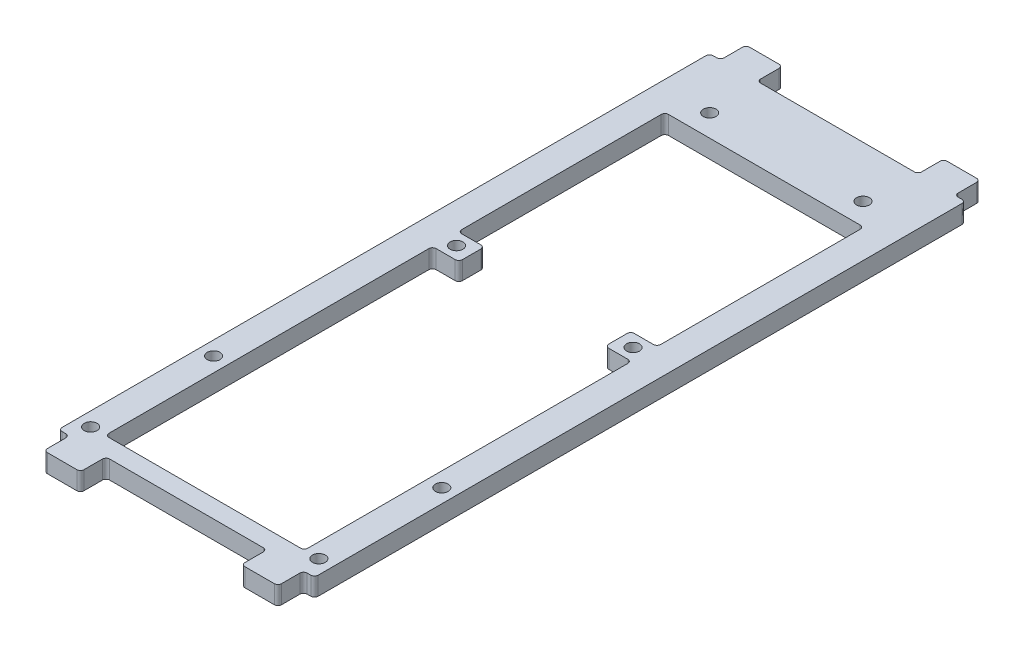
SolidWorks part; units mm, degrees
material "Acrylic (Medium-high impact)"
ref_plane "Front Plane" through (0, 0, 0) normal (0, 0, 1) x (1, 0, 0)
ref_plane "Top Plane" through (0, 0, 0) normal (0, 1, 0) x (1, 0, 0)
ref_plane "Right Plane" through (0, 0, 0) normal (1, 0, 0) x (0, 0, -1)
sketch "Sketch1" plane through (0, 0, 0) normal (0, 1, 0) x (1, 0, 0)
  line L0 (0, 0) -> (0, 34.093) construction
  line L5 (34, -89) -> (33, -89)
  line L6 (35, -88) -> (35, 88)
  line L27 (34, 89) -> (33, 89)
  line L28 (-35, -88) -> (-35, 88)
  line L29 (35, -89) -> (-35, 89) construction
  line L30 (35, 89) -> (-35, -89) construction
  line L32 (-32, 90) -> (-32, 95)
  line L33 (-31, 96) -> (-23, 96)
  line L34 (-22, 90) -> (-22, 95)
  line L35 (0, 0) -> (-23.5471, 0) construction
  line L36 (31, 96) -> (23, 96)
  line L37 (22, 90) -> (22, 95)
  line L38 (32, 90) -> (32, 95)
  line L39 (21, 89) -> (-21, 89)
  line L40 (-33, 89) -> (-34, 89)
  line L41 (32, -90) -> (32, -95)
  line L42 (31, -96) -> (23, -96)
  line L43 (22, -90) -> (22, -95)
  line L44 (-22, -90) -> (-22, -95)
  line L45 (-31, -96) -> (-23, -96)
  line L46 (-32, -90) -> (-32, -95)
  line L47 (-33, -89) -> (-34, -89)
  line L48 (21, -89) -> (-21, -89)
  arc A0 (22, -90) -> (21, -89) centre (21, -90) ccw
  arc A1 (23, -96) -> (22, -95) centre (23, -95) cw
  arc A2 (32, -95) -> (31, -96) centre (31, -95) cw
  arc A3 (32, -90) -> (33, -89) centre (33, -90) cw
  arc A4 (34, -89) -> (35, -88) centre (34, -88) ccw
  arc A5 (35, 88) -> (34, 89) centre (34, 88) ccw
  arc A6 (32, 90) -> (33, 89) centre (33, 90) ccw
  arc A7 (31, 96) -> (32, 95) centre (31, 95) cw
  arc A8 (23, 96) -> (22, 95) centre (23, 95) ccw
  arc A9 (22, 90) -> (21, 89) centre (21, 90) cw
  arc A10 (-21, 89) -> (-22, 90) centre (-21, 90) cw
  arc A11 (-23, 96) -> (-22, 95) centre (-23, 95) cw
  arc A12 (-32, 95) -> (-31, 96) centre (-31, 95) cw
  arc A13 (-33, 89) -> (-32, 90) centre (-33, 90) ccw
  arc A14 (-34, 89) -> (-35, 88) centre (-34, 88) ccw
  arc A15 (-34, -89) -> (-35, -88) centre (-34, -88) cw
  arc A16 (-32, -90) -> (-33, -89) centre (-33, -90) ccw
  arc A17 (-22, -90) -> (-21, -89) centre (-21, -90) cw
  arc A18 (-22, -95) -> (-23, -96) centre (-23, -95) cw
  arc A19 (-31, -96) -> (-32, -95) centre (-31, -95) cw
  point P0 (0, 0)
  point P27 (22, -89)
  point P30 (22, -96)
  point P33 (32, -96)
  point P36 (32, -89)
  point P45 (32, 89)
  point P48 (32, 96)
  point P51 (22, 96)
  point P54 (22, 89)
  point P57 (-22, 89)
  point P60 (-22, 96)
  point P63 (-32, 96)
  point P66 (-32, 89)
  point P75 (-32, -89)
  point P78 (-22, -89)
  point P81 (-22, -96)
  point P84 (-32, -96)
  dimension "D6" = 1
  dimension "D1" = 70
  dimension "D2" = 178
  dimension "D3" = 7
  dimension "D4" = 10
  dimension "D5" = 3
extrude "Boss-Extrude1" add sketch "Sketch1" along normal blind 5
sketch "Sketch2" plane through (0, 5, 0) normal (0, 1, 0) x (1, 0, 0)
  line L0 (0, 0) -> (0, -23.9489) construction
  circle A0 centre (-20.955, 75) radius 1.75
  circle A1 centre (-24.13, 8.96) radius 1.75
  circle A2 centre (20.955, 75) radius 1.75
  circle A3 centre (24.13, 8.96) radius 1.75
  dimension "D1" = 3.5
  dimension "D2" = 20.955
  dimension "D4" = 3.5
  dimension "D3" = 75
  dimension "D5" = 3.175
  dimension "D6" = 66.04
extrude "Cut-Extrude1" cut sketch "Sketch2" against normal blind 10
sketch "Sketch3" plane through (0, 5, 0) normal (0, 1, 0) x (1, 0, 0)
  line L0 (-21, -89) -> (21, -89) construction
  line L1 (-35, 88) -> (-35, -88) construction
  circle A0 centre (-31.2, -84) radius 1.75
  circle A1 centre (31.2, -84) radius 1.75
  circle A2 centre (31.2, -50.4) radius 1.75
  circle A3 centre (-31.2, -50.4) radius 1.75
  dimension "D1" = 3.5
  dimension "D2" = 5
  dimension "D3" = 3.8
  dimension "D4" = 2
  dimension "D5" = 2
extrude "Cut-Extrude2" cut sketch "Sketch3" against normal blind 10
sketch "Sketch4" plane through (0, 5, 0) normal (0, 1, 0) x (1, 0, 0)
  line L1 (-31.2, -84) -> (31.2, -84) construction
  line L2 (-31.2, -84) -> (-31.2, -50.4) construction
  line L3 (-31.2, -50.4) -> (31.2, -50.4) construction
  line L4 (31.2, -84) -> (31.2, -50.4) construction
  line L5 (-26.2, -84) -> (26.2, -84)
  line L6 (-27.2, -83) -> (-27.2, -72.4)
  line L7 (-27.2, -50.4) -> (27.2, -50.4)
  line L16 (-27.2, -50.4) -> (-27.2, -72.4)
  line L17 (27.2, -50.4) -> (27.2, -83)
  arc A0 (26.2, -84) -> (27.2, -83) centre (26.2, -83) ccw
  arc A1 (-26.2, -84) -> (-27.2, -83) centre (-26.2, -83) cw
  point P14 (27.2, -84)
  point P17 (-27.2, -84)
  dimension "D2" = 1
  dimension "D1" = 4
extrude "Cut-Extrude3" cut sketch "Sketch4" against normal blind 65
sketch "Sketch5" plane through (0, 5, 0) normal (0, 1, 0) x (1, 0, 0)
  line L0 (-27.2, -50.4) -> (27.2, -50.4)
  line L1 (-27.2, -50.4) -> (-27.2, -12.4)
  line L2 (27.2, -50.4) -> (27.2, -12.4)
  line L3 (-27.2, -12.4) -> (27.2, -12.4)
  line L7 (27.2, -50.4) -> (-27.2, -50.4) construction
  line L8 (-27.2, -50.4) -> (-27.2, -83) construction
  line L9 (27.2, -83) -> (27.2, -50.4) construction
  dimension "D1" = 38
extrude "Cut-Extrude4" cut sketch "Sketch5" against normal blind 5
sketch "Sketch6" plane through (0, 5, 0) normal (0, 1, 0) x (1, 0, 0)
  line L0 (-35, 88) -> (-35, -88) construction
  line L1 (26.2, 12.46) -> (21, 12.46)
  line L2 (27.2, 13.46) -> (27.2, 68)
  line L3 (26.2, 69) -> (-26.2, 69)
  line L4 (-27.2, 13.46) -> (-27.2, 68)
  line L5 (27.2, 12.46) -> (-27.2, 69) construction
  line L6 (27.2, 69) -> (-27.2, 12.46) construction
  line L7 (35, -88) -> (35, 88) construction
  line L8 (-20, 11.46) -> (-20, 6.46)
  line L10 (20, 6.46) -> (20, 11.46)
  line L11 (-21, 12.46) -> (-26.2, 12.46)
  line L12 (-20, -12.54) -> (16, -12.54)
  line L13 (-21, 5.46) -> (-26.2, 5.46)
  line L14 (-27.2, 4.46) -> (-27.2, -12.54)
  line L15 (-27.2, -12.54) -> (-20, -12.54)
  line L16 (21, 5.46) -> (26.2, 5.46)
  line L17 (27.2, 4.46) -> (27.2, -12.54)
  line L18 (27.2, -12.54) -> (16, -12.54)
  circle A0 centre (-24.13, 8.96) radius 1.75 construction
  circle A1 centre (-20.955, 75) radius 1.75 construction
  arc A2 (26.2, 5.46) -> (27.2, 4.46) centre (26.2, 4.46) cw
  arc A3 (27.2, 13.46) -> (26.2, 12.46) centre (26.2, 13.46) cw
  arc A4 (20, 11.46) -> (21, 12.46) centre (21, 11.46) cw
  arc A5 (21, 5.46) -> (20, 6.46) centre (21, 6.46) cw
  arc A6 (27.2, 68) -> (26.2, 69) centre (26.2, 68) ccw
  arc A7 (-26.2, 69) -> (-27.2, 68) centre (-26.2, 68) ccw
  arc A8 (-26.2, 12.46) -> (-27.2, 13.46) centre (-26.2, 13.46) cw
  arc A9 (-26.2, 5.46) -> (-27.2, 4.46) centre (-26.2, 4.46) ccw
  arc A10 (-21, 5.46) -> (-20, 6.46) centre (-21, 6.46) ccw
  arc A11 (-20, 11.46) -> (-21, 12.46) centre (-21, 11.46) ccw
  point P0 (0, 40.73)
  point P46 (-20, 5.46)
  point P49 (-20, 12.46)
  dimension "D12" = 1
  dimension "D1" = 6
  dimension "D2" = 3.5
  dimension "D3" = 7.8
  dimension "D4" = 7.8
  dimension "D5" = 36
  dimension "D6" = 20
  dimension "D7" = 25
  dimension "D8" = 7
  dimension "D9" = 0
  dimension "D10" = 20
  dimension "D11" = 0
extrude "Cut-Extrude5" cut sketch "Sketch6" against normal blind 5
